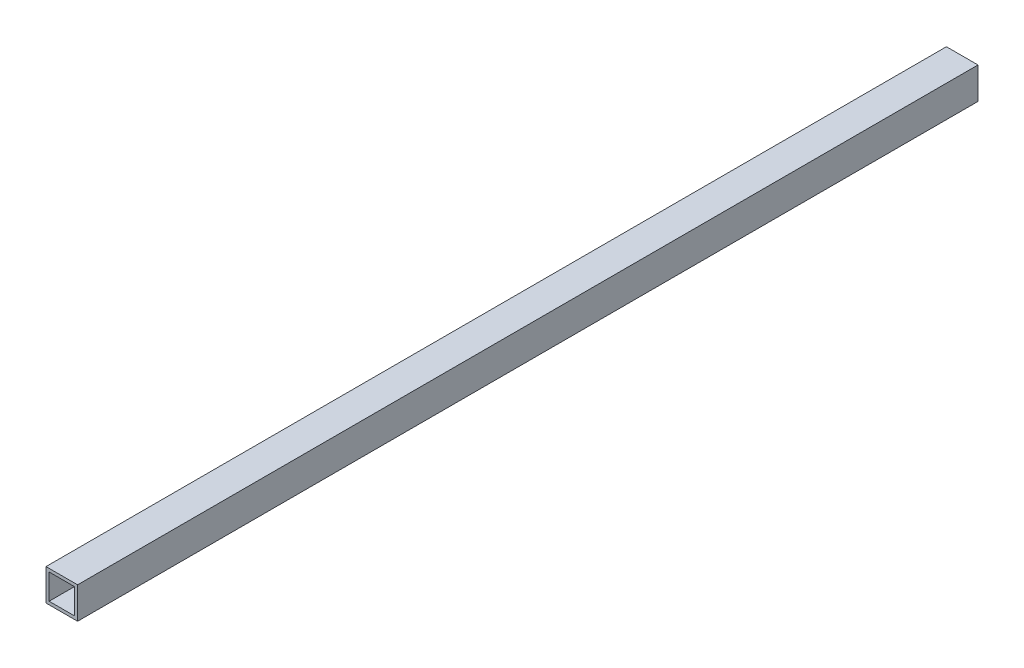
SolidWorks part; units mm, degrees
material "6061 Alloy"
ref_plane "Front Plane" through (0, 0, 0) normal (0, 0, 1) x (1, 0, 0)
ref_plane "Top Plane" through (0, 0, 0) normal (0, 1, 0) x (1, 0, 0)
ref_plane "Right Plane" through (0, 0, 0) normal (1, 0, 0) x (0, 0, -1)
sketch "Sketch1" plane through (0, 0, 0) normal (0, 0, 1) x (1, 0, 0)
  line L1 (-10, 10) -> (10, 10)
  line L2 (-10, 10) -> (-10, -10)
  line L3 (-10, -10) -> (10, -10)
  line L4 (10, 10) -> (10, -10)
  line L5 (-10, 10) -> (10, -10) construction
  line L6 (-10, -10) -> (10, 10) construction
  line L7 (-8.0211, 8.0211) -> (8.0211, 8.0211)
  line L8 (-8.0211, 8.0211) -> (-8.0211, -8.0211)
  line L9 (-8.0211, -8.0211) -> (8.0211, -8.0211)
  line L10 (8.0211, 8.0211) -> (8.0211, -8.0211)
  line L11 (-8.0211, 8.0211) -> (8.0211, -8.0211) construction
  line L12 (-8.0211, -8.0211) -> (8.0211, 8.0211) construction
  point P0 (0, 0)
  point P6 (0, 0)
extrude "Boss-Extrude1" add sketch "Sketch1" along normal blind 570
